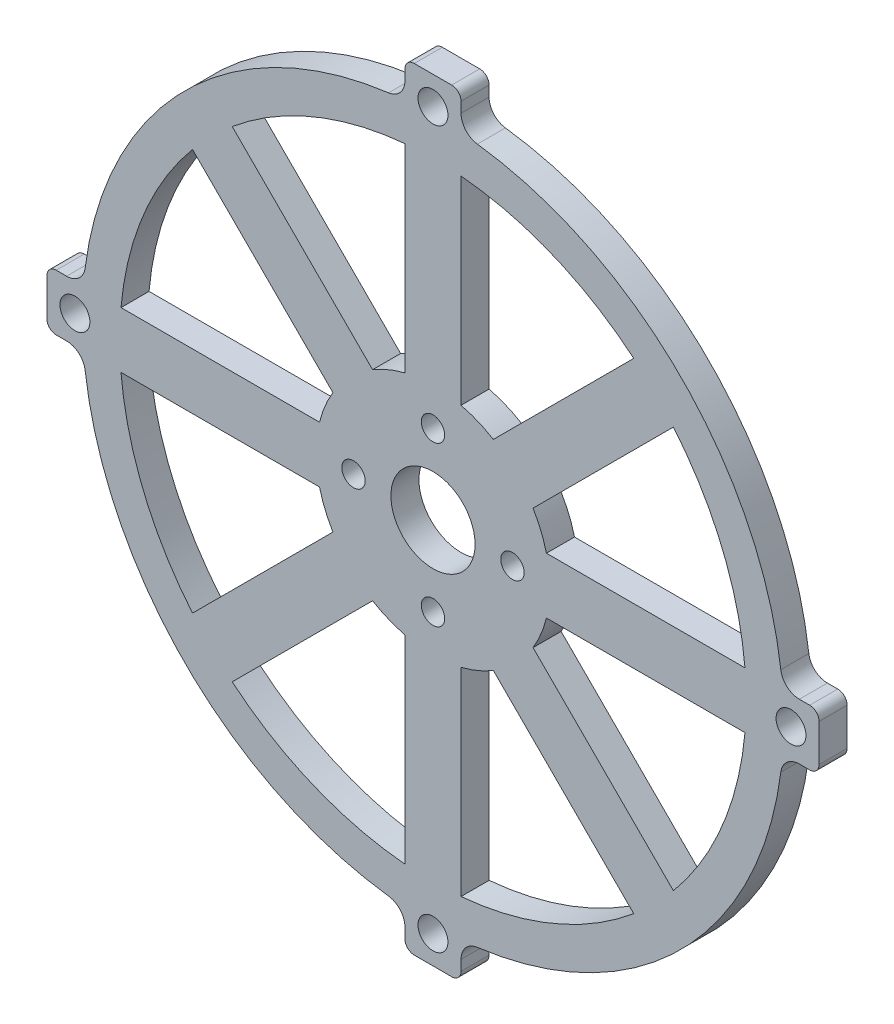
SolidWorks part; units mm, degrees
ref_plane "正面" through (0, 0, 0) normal (0, 0, 1) x (1, 0, 0)
ref_plane "平面" through (0, 0, 0) normal (0, 1, 0) x (1, 0, 0)
ref_plane "右側面" through (0, 0, 0) normal (1, 0, 0) x (0, 0, -1)
sketch "ｽｹｯﾁ1" plane through (0, 0, 0) normal (0, 0, 1) x (1, 0, 0)
  line L12 (-3, -39.1823) -> (-3, -41.2916)
  line L13 (-3, -41.2916) -> (3, -41.2916)
  line L14 (3, -41.2916) -> (3, -39.1823)
  line L15 (39.1823, -3) -> (41.2916, -3)
  line L16 (41.2916, -3) -> (41.2916, 3)
  line L17 (41.2916, 3) -> (39.1823, 3)
  line L18 (3, 39.1823) -> (3, 41.2916)
  line L19 (3, 41.2916) -> (-3, 41.2916)
  line L20 (-3, 41.2916) -> (-3, 39.1823)
  line L21 (-39.1823, 3) -> (-41.2916, 3)
  line L22 (-41.2916, 3) -> (-41.2916, -3)
  line L23 (-41.2916, -3) -> (-39.1823, -3)
  line L24 (-3, -39.1823) -> (-3, -41.2916)
  line L25 (-3, -41.2916) -> (3, -41.2916)
  line L26 (3, -41.2916) -> (3, -39.1823)
  line L27 (39.1823, -3) -> (41.2916, -3)
  line L28 (41.2916, -3) -> (41.2916, 3)
  line L29 (41.2916, 3) -> (39.1823, 3)
  line L30 (3, 39.1823) -> (3, 41.2916)
  line L31 (3, 41.2916) -> (-3, 41.2916)
  line L32 (-3, 41.2916) -> (-3, 39.1823)
  line L33 (-39.1823, 3) -> (-41.2916, 3)
  line L34 (-41.2916, 3) -> (-41.2916, -3)
  line L35 (-41.2916, -3) -> (-39.1823, -3)
  circle A0 centre (-38.2916, 0) radius 1.6 construction
  circle A1 centre (0, -38.2916) radius 1.6 construction
  circle A2 centre (0, 38.2916) radius 1.6 construction
  circle A3 centre (38.2916, 0) radius 1.6 construction
  circle A4 centre (-38.2916, 0) radius 1.6
  circle A5 centre (0, -38.2916) radius 1.6
  circle A6 centre (0, 38.2916) radius 1.6
  circle A7 centre (38.2916, 0) radius 1.6
  arc A12 (-3, -39.1823) -> (-4.7468, -37.1984) centre (-5, -39.1823) ccw
  arc A13 (4.7468, -37.1984) -> (3, -39.1823) centre (5, -39.1823) ccw
  arc A14 (4.7468, -37.1984) -> (37.1984, -4.7468) centre (0, 0) ccw
  arc A15 (39.1823, -3) -> (37.1984, -4.7468) centre (39.1823, -5) ccw
  arc A16 (37.1984, 4.7468) -> (39.1823, 3) centre (39.1823, 5) ccw
  arc A17 (37.1984, 4.7468) -> (4.7468, 37.1984) centre (0, 0) ccw
  arc A18 (3, 39.1823) -> (4.7468, 37.1984) centre (5, 39.1823) ccw
  arc A19 (-4.7468, 37.1984) -> (-3, 39.1823) centre (-5, 39.1823) ccw
  arc A20 (-4.7468, 37.1984) -> (-37.1984, 4.7468) centre (0, 0) ccw
  arc A21 (-39.1823, 3) -> (-37.1984, 4.7468) centre (-39.1823, 5) ccw
  arc A22 (-37.1984, -4.7468) -> (-39.1823, -3) centre (-39.1823, -5) ccw
  arc A23 (-37.1984, -4.7468) -> (-4.7468, -37.1984) centre (0, 0) ccw
  arc A24 (-3, -39.1823) -> (-4.7468, -37.1984) centre (-5, -39.1823) ccw
  arc A25 (4.7468, -37.1984) -> (3, -39.1823) centre (5, -39.1823) ccw
  arc A26 (4.7468, -37.1984) -> (37.1984, -4.7468) centre (0, 0) ccw
  arc A27 (39.1823, -3) -> (37.1984, -4.7468) centre (39.1823, -5) ccw
  arc A28 (37.1984, 4.7468) -> (39.1823, 3) centre (39.1823, 5) ccw
  arc A29 (37.1984, 4.7468) -> (4.7468, 37.1984) centre (0, 0) ccw
  arc A30 (3, 39.1823) -> (4.7468, 37.1984) centre (5, 39.1823) ccw
  arc A31 (-4.7468, 37.1984) -> (-3, 39.1823) centre (-5, 39.1823) ccw
  arc A32 (-4.7468, 37.1984) -> (-37.1984, 4.7468) centre (0, 0) ccw
  arc A33 (-39.1823, 3) -> (-37.1984, 4.7468) centre (-39.1823, 5) ccw
  arc A34 (-37.1984, -4.7468) -> (-39.1823, -3) centre (-39.1823, -5) ccw
  arc A35 (-37.1984, -4.7468) -> (-4.7468, -37.1984) centre (0, 0) ccw
  dimension "D1" = 0
extrude "ﾎﾞｽ - 押し出し1" add sketch "ｽｹｯﾁ1" along normal blind 3
sketch "ｽｹｯﾁ3" plane through (0, 0, 3) normal (0, 0, 1) x (1, 0, 0)
  circle A0 centre (0, 0) radius 4.5
  circle A1 centre (0, 8.5) radius 1.25
  circle A2 centre (8.5, 0) radius 1.25
  circle A3 centre (0, -8.5) radius 1.25
  circle A4 centre (-8.5, 0) radius 1.25
  point P14 (0, 0)
  dimension "D1" = 9
  dimension "D2" = 2.5
  dimension "D3" = 8.5
  dimension "D4" = 4
extrude "ｶｯﾄ - 押し出し1" cut sketch "ｽｹｯﾁ3" against normal through all
sketch "ｽｹｯﾁ4" plane through (0, 0, 3) normal (0, 0, 1) x (1, 0, 0)
  line L0 (0, 33.5) -> (0, 0) construction
  line L1 (-3, 33.3654) -> (-3, 12.1347)
  line L2 (3, 33.3654) -> (3, 12.1347)
  line L3 (33.3654, 3) -> (12.1347, 3)
  line L4 (33.3654, -3) -> (12.1347, -3)
  line L5 (3, -33.3654) -> (3, -12.1347)
  line L6 (-3, -33.3654) -> (-3, -12.1347)
  line L7 (-33.3654, -3) -> (-12.1347, -3)
  line L8 (-33.3654, 3) -> (-12.1347, 3)
  line L9 (-21.4716, 25.7142) -> (-6.4592, 10.7018)
  line L10 (-25.7142, 21.4716) -> (-10.7018, 6.4592)
  line L11 (-25.7142, -21.4716) -> (-10.7018, -6.4592)
  line L12 (-21.4716, -25.7142) -> (-6.4592, -10.7018)
  line L13 (21.4716, -25.7142) -> (6.4592, -10.7018)
  line L14 (25.7142, -21.4716) -> (10.7018, -6.4592)
  line L15 (25.7142, 21.4716) -> (10.7018, 6.4592)
  line L16 (21.4716, 25.7142) -> (6.4592, 10.7018)
  arc A0 (-3, 12.1347) -> (-6.4592, 10.7018) centre (0, 0) ccw
  arc A1 (-3, 33.3654) -> (-21.4716, 25.7142) centre (0, 0) ccw
  arc A2 (37.1984, 4.7468) -> (4.7468, 37.1984) centre (0, 0) ccw construction
  arc A3 (33.3654, 3) -> (25.7142, 21.4716) centre (0, 0) ccw
  arc A4 (12.1347, 3) -> (10.7018, 6.4592) centre (0, 0) ccw
  arc A5 (3, -12.1347) -> (6.4592, -10.7018) centre (0, 0) ccw
  arc A6 (3, -33.3654) -> (21.4716, -25.7142) centre (0, 0) ccw
  arc A7 (-12.1347, -3) -> (-10.7018, -6.4592) centre (0, 0) ccw
  arc A8 (-33.3654, -3) -> (-25.7142, -21.4716) centre (0, 0) ccw
  arc A9 (-6.4592, -10.7018) -> (-3, -12.1347) centre (0, 0) ccw
  arc A10 (-21.4716, -25.7142) -> (-3, -33.3654) centre (0, 0) ccw
  arc A11 (10.7018, -6.4592) -> (12.1347, -3) centre (0, 0) ccw
  arc A12 (25.7142, -21.4716) -> (33.3654, -3) centre (0, 0) ccw
  arc A13 (6.4592, 10.7018) -> (3, 12.1347) centre (0, 0) ccw
  arc A14 (21.4716, 25.7142) -> (3, 33.3654) centre (0, 0) ccw
  arc A15 (-10.7018, 6.4592) -> (-12.1347, 3) centre (0, 0) ccw
  arc A16 (-25.7142, 21.4716) -> (-33.3654, 3) centre (0, 0) ccw
  point P27 (0, 0)
  point P41 (0, 0)
  dimension "D3" = 4
  dimension "D4" = 25
  dimension "D1" = 3
  dimension "D2" = 3
  dimension "D5" = 4
  dimension "D6" = 2
extrude "ｶｯﾄ - 押し出し2" cut sketch "ｽｹｯﾁ4" against normal through all
fillet "ﾌｨﾚｯﾄ1" radius 1 8 edges at (41.2916, 3, 1.5) (41.2916, -3, 1.5) (3, -41.2916, 1.5) (-3, -41.2916, 1.5) (-41.2916, -3, 1.5) (-41.2916, 3, 1.5) (-3, 41.2916, 1.5) (3, 41.2916, 1.5)
